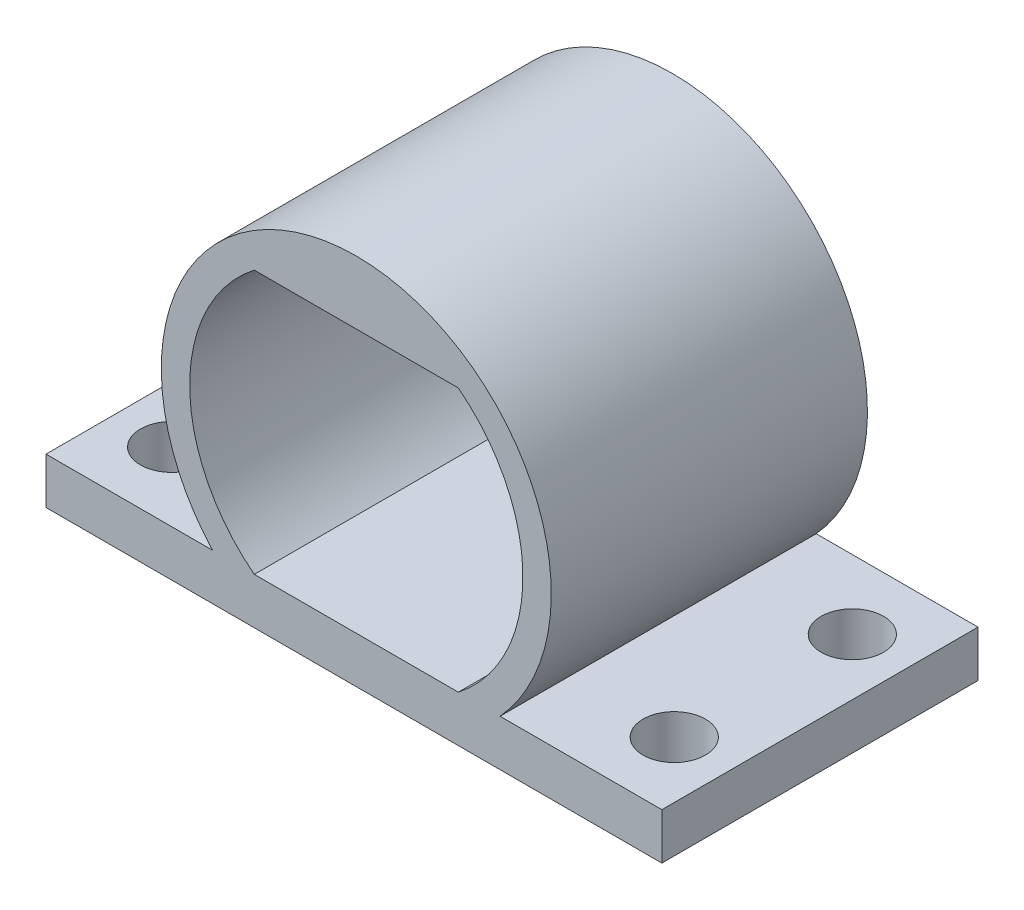
SolidWorks part; units mm, degrees
ref_plane "Front" through (0, 0, 0) normal (0, 0, 1) x (1, 0, 0)
ref_plane "Top" through (0, 0, 0) normal (0, 1, 0) x (1, 0, 0)
ref_plane "Right" through (0, 0, 0) normal (1, 0, 0) x (0, 0, -1)
sketch "Sketch1" plane through (0, 0, 0) normal (0, 0, 1) x (1, 0, 0)
  line L0 (-19.17, 0) -> (-9.4011, 0) construction
  line L1 (-3.4066, -5) -> (-3.4066, 5) construction
  line L2 (-3.4066, -5) -> (3.2266, -5)
  line L3 (-3.4066, 5) -> (3.2266, 5)
  line L4 (-0.09, -5) -> (-0.09, 5) construction
  line L5 (5.91, 0) -> (18.99, 0) construction
  line L6 (-3.4, -6) -> (3.22, -6)
  line L7 (-3.4, -6) -> (-11.7771, -6)
  line L8 (-11.7771, -6) -> (-11.7771, -5)
  line L9 (-11.7771, -5) -> (-3.4066, -5)
  line L10 (-10.6296, -5) -> (-7.9329, -5) construction
  line L11 (-10.6296, -5) -> (-10.6296, -6) construction
  line L12 (-7.9329, -5) -> (-7.9329, -6) construction
  line L13 (7.7529, -5) -> (7.7529, -6) construction
  line L14 (10.4496, -5) -> (10.4496, -6) construction
  line L15 (3.22, -6) -> (11.5971, -6)
  line L16 (11.5971, -6) -> (11.5971, -5)
  line L17 (11.5971, -5) -> (3.2266, -5)
  arc A0 (3.2266, -5) -> (3.2266, 5) centre (-0.09, 0) ccw
  arc A1 (-3.4066, 5) -> (-3.4066, -5) centre (-0.09, 0) ccw
  arc A2 (3.22, -6) -> (-3.4, -6) centre (-0.09, 0) ccw
  dimension "D1" = 12
  dimension "D2" = 10
  dimension "D3" = 2.6968
extrude "Boss-Extrude1" add sketch "Sketch1" along normal blind 12 contours L17 A2 L9 A1 L3 A0 | A2 L15 L16 L17 | L9 A2 L6 L17 L2 | A2 L9 L8 L7
sketch "Sketch3" plane through (0, -5, 0) normal (0, 1, 0) x (1, 0, 0)
  line L0 (-0.09, -12) -> (-0.09, 0) construction
  line L1 (-9.6272, 0) -> (-9.6272, -12) construction
  line L2 (-11.7771, 0) -> (-4.7757, 0) construction
  line L3 (-11.7771, -12) -> (-4.7757, -12) construction
  line L4 (-6.9425, -12) -> (6.7625, -12) construction
  line L5 (6.7625, 0) -> (-6.9425, 0) construction
  line L6 (-9.6272, -6) -> (9.4472, -6) construction
  circle A0 centre (-9.6272, -9.3798) radius 1.1847
  circle A1 centre (9.4472, -9.3798) radius 1.1847
  circle A2 centre (9.4472, -2.6202) radius 1.1847
  circle A3 centre (-9.6272, -2.6202) radius 1.1847
  point P8 (-9.6272, -6)
extrude "Cut-Extrude3" cut sketch "Sketch3" against normal blind 5
sketch "Sketch6" plane through (0, -5, 0) normal (0, 1, 0) x (1, 0, 0)
  line L2 (-9.6272, -1.4355) -> (-9.6272, 0) construction
  line L3 (-11.7771, 0) -> (-4.7757, 0) construction
  line L4 (-10.8119, -2.6202) -> (-11.7771, -2.6202) construction
  line L5 (-11.7771, -12) -> (-11.7771, 0) construction
  line L6 (-10.8119, -2.6202) -> (-9.6272, -2.6202) construction
  line L7 (-9.6272, -2.6202) -> (-9.6272, -1.2066) construction
  circle A0 centre (-9.6272, -2.6202) radius 1.1847 construction
  dimension "D1" = 2.1499
  dimension "D2" = 2.6202
sketch "Sketch7" plane through (0, 0, 12) normal (0, 0, 1) x (1, 0, 0)
  line L1 (0, 0) -> (-0.0692, 6.0746) construction
  line L2 (-11.7771, -6) -> (-11.7771, -6.7565)
  line L3 (-11.7771, -6.7565) -> (11.5971, -6.7565)
  line L4 (11.5971, -6.7565) -> (11.5971, -6)
  line L6 (-11.7771, -6) -> (-11.7771, -5)
  line L7 (-11.7771, -5) -> (11.5971, -5)
  line L8 (11.5971, -5) -> (11.5971, -6)
  line L10 (-3.4505, 5) -> (3.4505, 5)
  arc A0 (3.0199, -6.7565) -> (-3.0199, -6.7565) centre (0, 0) ccw
  arc A1 (3.4505, -5) -> (-3.4505, -5) centre (0, 0) ccw
  arc A3 (-3.4066, 5) -> (-3.4066, -5) centre (-0.09, 0) ccw construction
  arc A4 (3.2266, -5) -> (3.2266, 5) centre (-0.09, 0) ccw construction
  line M5 (-11.7771, -6) -> (11.5971, -6)
  arc M8 (4.5957, -5) -> (-4.7757, -5) centre (-0.09, 0) ccw
  line M9 (-4.7757, -5) -> (-11.7771, -5)
  dimension "D1" = 12.15
  dimension "D2" = 6.0746
extrude "Boss-Extrude6" add sketch "Sketch7" against normal blind 12 contours L7 A0 M9 M8 | A0 L2 L3 M5 | A0 L3 M5 | A0 L3 L4 M5
sketch "Sketch9" plane through (0, 0, 12) normal (0, 0, 1) x (1, 0, 0)
  line L1 (-3.4768, 5) -> (3.4768, 5)
  line L3 (-3.4768, -5) -> (3.4768, -5)
  arc A0 (3.4768, -5) -> (3.4768, 5) centre (0, 0) ccw
  arc A1 (-3.4768, 5) -> (-3.4768, -5) centre (0, 0) ccw
extrude "Cut-Extrude4" cut sketch "Sketch9" against normal blind 12
sketch "Sketch10" plane through (0, -5, 0) normal (0, 1, 0) x (1, 0, 0)
  line L0 (7.4006, 0) -> (-7.4006, 0) construction
  line L2 (0, 0) -> (0, -12) construction
  line L3 (-11.7771, -12) -> (-11.7771, 0) construction
  line L4 (-11.7771, -6) -> (11.5971, -6) construction
  line L5 (11.5971, -12) -> (11.5971, 0) construction
  line L6 (-7.4006, -12) -> (7.4006, -12) construction
  circle A0 centre (-9.6272, -2.6202) radius 1.1847
  circle A1 centre (-9.6272, -9.3798) radius 1.1847
  circle A2 centre (9.4472, -2.6202) radius 1.1847
  circle A3 centre (9.4472, -9.3798) radius 1.1847
  point P3 (0, 0)
extrude "Cut-Extrude5" cut sketch "Sketch10" against normal blind 12
sketch "Sketch11" plane through (0, 0, 12) normal (0, 0, 1) x (1, 0, 0)
  line L0 (-3.4768, 5) -> (-3.8718, 5)
  line L1 (-3.4768, 5) -> (3.8718, 5)
  line L2 (-3.4768, -5) -> (-3.8718, -5)
  line L3 (-3.4768, -5) -> (3.8718, -5)
  arc A0 (3.8718, -5) -> (3.8718, 5) centre (0, 0) ccw
  arc A1 (-3.8718, 5) -> (-3.8718, -5) centre (0, 0) ccw
  dimension "D1" = 12.6476
extrude "Cut-Extrude7" cut sketch "Sketch11" against normal blind 19
